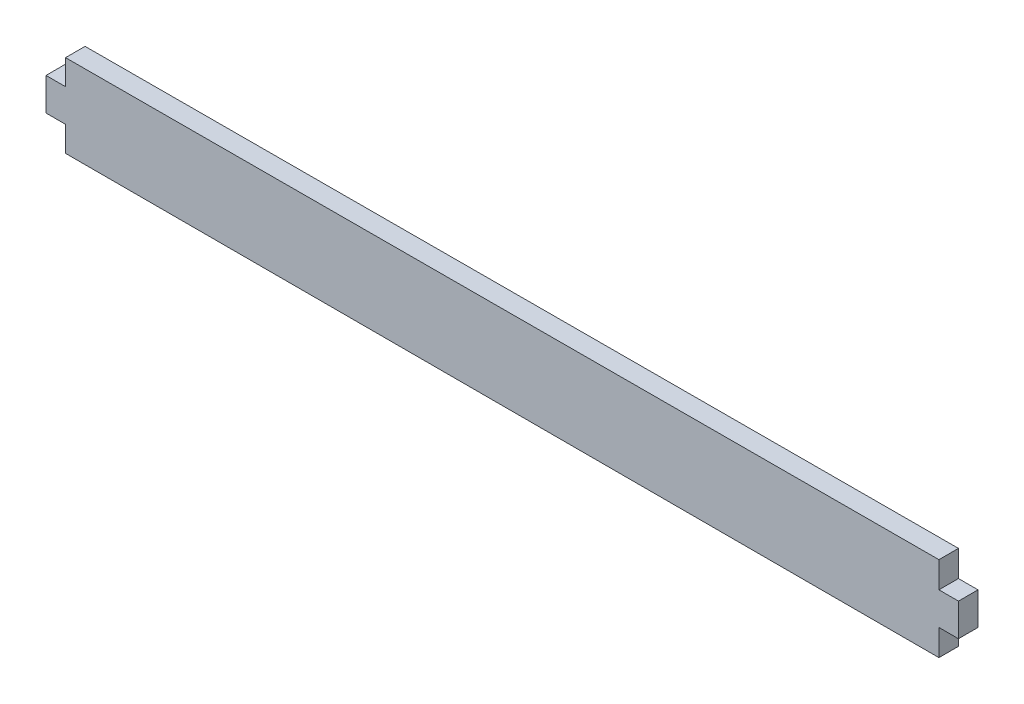
SolidWorks part; units mm, degrees
ref_plane "Front Plane" through (0, 0, 0) normal (0, 0, 1) x (1, 0, 0)
ref_plane "Top Plane" through (0, 0, 0) normal (0, 1, 0) x (1, 0, 0)
ref_plane "Right Plane" through (0, 0, 0) normal (1, 0, 0) x (0, 0, -1)
sketch "Sketch1" plane through (0, 0, 0) normal (0, 0, 1) x (1, 0, 0)
  line L0 (-195.1342, 44.2621) -> (-204.4805, 44.2621) construction
  line L1 (-209.1342, 4.7936) -> (58.8275, 4.7936)
  line L2 (-209.1342, 4.7936) -> (-209.1342, 30.235)
  line L3 (58.8275, 17.8128) -> (-209.1342, 17.5143) construction
  line L4 (58.8275, 4.7936) -> (58.8275, 30.8319)
  line L5 (-195.0596, 35.2943) -> (-202.3632, 35.2943) construction
  line L6 (-75.1534, 53.6601) -> (-75.1534, 4.7936) construction
  line L8 (58.8275, 30.8319) -> (-209.1342, 30.235)
  line L9 (44.6564, 0.0328) -> (52.0122, 0.0328) construction
  line B0 (-215.1286, 17.5143) -> (-209.1342, 17.5143) construction
  line B1 (-215.1286, 12.5143) -> (-215.1286, 22.5143)
  line B2 (-215.1286, 12.5143) -> (-209.1342, 12.5143)
  line B3 (-209.1342, 12.5143) -> (-209.1342, 22.5143)
  line B4 (-215.1286, 22.5143) -> (-209.1342, 22.5143)
  line B5 (58.8275, 17.8128) -> (64.8219, 17.8128) construction
  line B6 (58.8275, 12.8128) -> (58.8275, 22.8128)
  line B7 (58.8275, 12.8128) -> (64.8219, 12.8128)
  line B8 (64.8219, 12.8128) -> (64.8219, 22.8128)
  line B9 (58.8275, 22.8128) -> (64.8219, 22.8128)
  line B10 (-209.1342, 41.767) -> (-199.1342, 41.767)
  line B11 (-199.1342, 41.767) -> (-199.1342, 39.307)
  line B12 (-199.1342, 39.307) -> (-195.1342, 39.2621)
  line B13 (-195.1342, 39.2621) -> (-195.1342, 49.2621)
  line B14 (-195.1342, 49.2621) -> (-199.1342, 49.307)
  line B15 (-199.1342, 49.307) -> (-199.1342, 46.847)
  line B16 (-199.1342, 46.847) -> (-209.1342, 46.847)
  line B17 (58.8275, 42.6255) -> (48.8275, 42.6255)
  line B18 (48.8275, 42.6255) -> (48.8275, 45.0855)
  line B19 (48.8275, 45.0855) -> (44.8275, 45.1304)
  line B20 (44.8275, 45.1304) -> (44.8275, 35.1304)
  line B21 (44.8275, 35.1304) -> (48.8275, 35.0855)
  line B22 (48.8275, 35.0855) -> (48.8275, 37.5455)
  line B23 (48.8275, 37.5455) -> (58.8275, 37.5455)
  dimension "D5" = 17.78
  dimension "D7" = 17.78
sketch_block_instance "Block1-6"
sketch_block "Block1" parameters "D1"=4.2151, "D2"=10.103, "D3"=7.4845
sketch_block_instance "Block1-8"
sketch_block_instance "Block1-10"
sketch_block_instance "extrusionblock-2"
sketch_block "extrusionblock" parameters "D1"=5.9944, "D2"=10
sketch_block_instance "extrusionblock-4"
sketch_block_instance "screwblock-2"
sketch_block "screwblock" parameters "D1"=4.2151, "D2"=10.103, "D3"=7.4845, "D4"=1.829
sketch_block_instance "screwblock-4"
extrude "Extrude1" add sketch "Sketch1" along normal blind 5.9944
